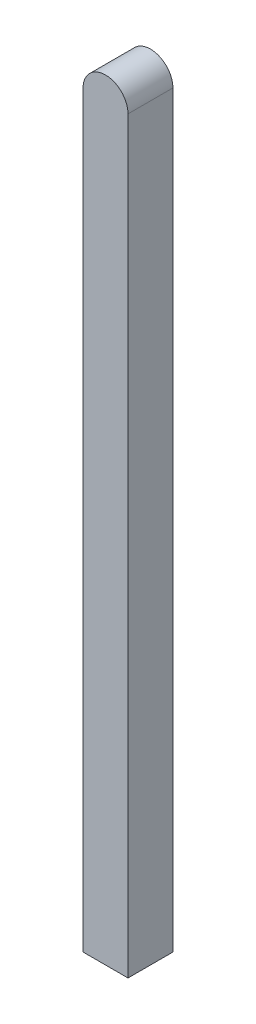
SolidWorks part; units mm, degrees
ref_plane "Front Plane" through (0, 0, 0) normal (0, 0, 1) x (1, 0, 0)
ref_plane "Top Plane" through (0, 0, 0) normal (0, 1, 0) x (1, 0, 0)
ref_plane "Right Plane" through (0, 0, 0) normal (1, 0, 0) x (0, 0, -1)
sketch "Sketch1" plane through (0, 0, 0) normal (0, 1, 0) x (1, 0, 0)
  line L1 (-15, 15) -> (15, 15)
  line L2 (-15, 15) -> (-15, -15)
  line L3 (-15, -15) -> (15, -15)
  line L4 (15, 15) -> (15, -15)
  line L5 (-15, 15) -> (15, -15) construction
  line L6 (-15, -15) -> (15, 15) construction
  point P0 (0, 0)
  dimension "D1" = 30
  dimension "D2" = 30
extrude "Boss-Extrude1" add sketch "Sketch1" along normal blind 500
sketch "Sketch2" plane through (0, 0, 15) normal (0, 0, 1) x (1, 0, 0)
  line L1 (-15, 500) -> (15, 500) construction
  circle A1 centre (0, 500) radius 15
extrude "Boss-Extrude2" add sketch "Sketch2" against normal blind 30
sketch "Sketch4" plane through (0, 0, 0) normal (0, -1, 0) x (1, 0, 0)
  circle A0 centre (0, 0) radius 10
  dimension "D1" = 20
extrude "Cut-Extrude1" cut sketch "Sketch4" against normal blind 50
